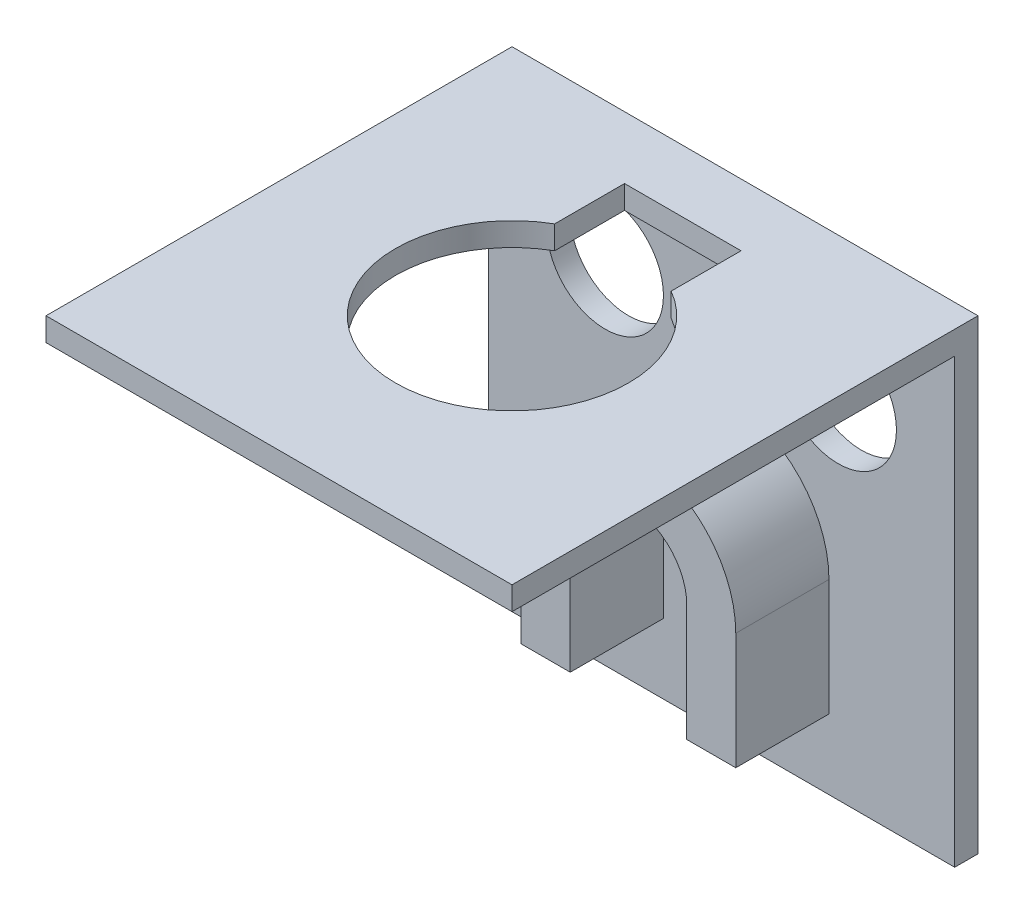
SolidWorks part; units mm, degrees
ref_plane "Front Plane" through (0, 0, 0) normal (0, 0, 1) x (1, 0, 0)
ref_plane "Top Plane" through (0, 0, 0) normal (0, 1, 0) x (1, 0, 0)
ref_plane "Right Plane" through (0, 0, 0) normal (1, 0, 0) x (0, 0, -1)
sketch "Sketch2" plane through (0, 0, 0) normal (0, 0, 1) x (1, 0, 0)
  line L1 (0, 0) -> (20, 0)
  line L2 (0, 0) -> (0, 20)
  line L3 (0, 20) -> (20, 20)
  line L4 (20, 0) -> (20, 20)
  dimension "D1" = 20
  dimension "D2" = 20
extrude "Boss-Extrude1" add sketch "Sketch2" along normal blind 20
sketch "Sketch3" plane through (0, 0, 20) normal (0, 0, 1) x (1, 0, 0)
  line L0 (20, 0) -> (20, 20) construction
  line L1 (0, 0) -> (20, 0)
  line L2 (0, 0) -> (0, 19)
  line L3 (0, 19) -> (20, 19)
  line L4 (20, 0) -> (20, 19)
  dimension "D1" = 19
extrude "Cut-Extrude1" cut sketch "Sketch3" against normal blind 19
sketch "Sketch4" plane through (0, 19, 0) normal (0, -1, 0) x (1, 0, 0)
  line L1 (0, 1) -> (0, 20) construction
  circle A0 centre (10, 10) radius 5
  dimension "D1" = 10
  dimension "D2" = 10
  dimension "D3" = 10
extrude "Cut-Extrude2" cut sketch "Sketch4" against normal blind 17.5
sketch "Sketch6" plane through (0, 0, 1) normal (0, 0, 1) x (1, 0, 0)
  line L0 (7.5, 3) -> (7.5, 8)
  line L1 (12.5, 8) -> (12.5, 3)
  line L2 (0, 19) -> (0, 0) construction
  line L3 (7.5, 3) -> (5.3965, 3)
  line L4 (5.3965, 3) -> (5.3965, 8)
  line L5 (12.5, 3) -> (14.6035, 3)
  line L6 (14.6035, 3) -> (14.6035, 8)
  arc A0 (7.5, 8) -> (12.5, 8) centre (10, 8) cw
  arc A1 (5.3965, 8) -> (14.6035, 8) centre (10, 8) cw
  dimension "D1" = 2.5
  dimension "D2" = 5
  dimension "D3" = 10
  dimension "D4" = 8
  dimension "D5" = 5
  dimension "D6" = 5
  dimension "D7" = 3
  dimension "D8" = 2.1035
  dimension "D9" = 0
extrude "Boss-Extrude2" add sketch "Sketch6" along normal blind 4
sketch "Sketch10" plane through (0, 0, 1) normal (0, 0, 1) x (1, 0, 0)
  line L0 (5, 15) -> (15, 15) construction
  line L1 (0, 19) -> (0, 0) construction
  circle A0 centre (5, 15) radius 2.5
  circle A1 centre (15, 15) radius 2.5
  point P6 (0, 0)
  dimension "D3" = 5
  dimension "D4" = 5
  dimension "D1" = 10
  dimension "D2" = 5
  dimension "D5" = 15
extrude "Cut-Extrude3" cut sketch "Sketch10" against normal through all
sketch "Sketch11" plane through (0, 20, 0) normal (0, 1, 0) x (1, 0, 0)
  line L0 (7.5, -5.6699) -> (7.5, -2.6699)
  line L1 (12.5, -5.6699) -> (12.5, -2.6699)
  line L3 (7.5, -2.6699) -> (12.5, -2.6699)
  circle A0 centre (10, -10) radius 5 construction
  arc A1 (7.5, -5.6699) -> (12.5, -5.6699) centre (10, -10) cw
  dimension "D4" = 5
  dimension "D1" = 5
  dimension "D2" = 3
  dimension "D3" = 3
extrude "Cut-Extrude4" cut sketch "Sketch11" against normal blind 2
